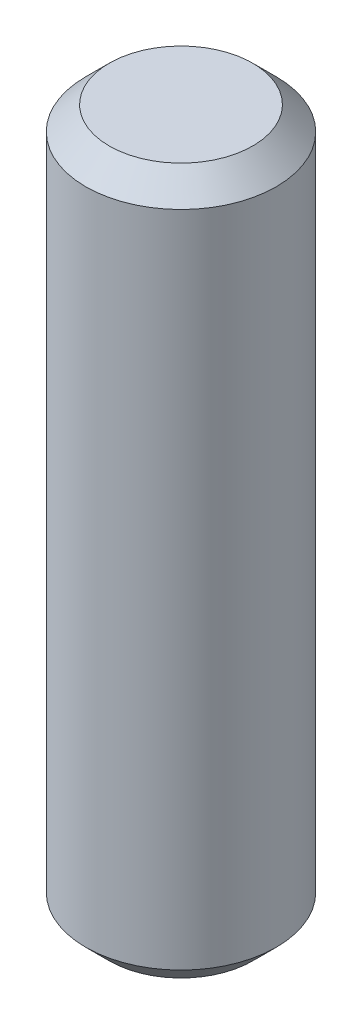
SolidWorks part; units mm, degrees
ref_plane "Front Plane" through (0, 0, 0) normal (0, 0, 1) x (1, 0, 0)
ref_plane "Top Plane" through (0, 0, 0) normal (0, 1, 0) x (1, 0, 0)
ref_plane "Right Plane" through (0, 0, 0) normal (1, 0, 0) x (0, 0, -1)
sketch "Sketch1" plane through (0, 0, 0) normal (0, 1, 0) x (1, 0, 0)
  circle A0 centre (0, 0) radius 4.05
  dimension "D1" = 8.1
extrude "Boss-Extrude1" add sketch "Sketch1" along normal mid plane 30
chamfer "Chamfer1" distance 1 angle 45 2 edges at (0, -15, 4.05) (0, 15, 4.05)
